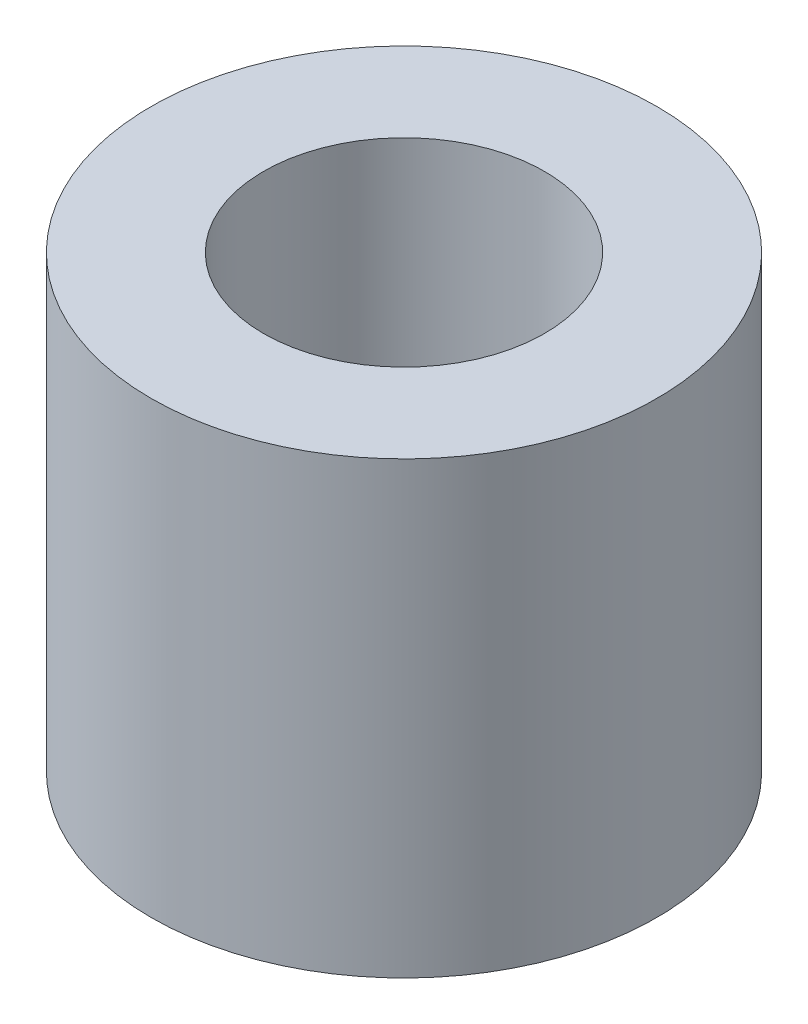
SolidWorks part; units mm, degrees
ref_plane "Front Plane" through (0, 0, 0) normal (0, 0, 1) x (1, 0, 0)
ref_plane "Top Plane" through (0, 0, 0) normal (0, 1, 0) x (1, 0, 0)
ref_plane "Right Plane" through (0, 0, 0) normal (1, 0, 0) x (0, 0, -1)
sketch "Sketch1" plane through (0, 0, 0) normal (0, 1, 0) x (1, 0, 0)
  circle A0 centre (0, 0) radius 4.5
  circle A1 centre (0, 0) radius 2.5
  dimension "D1" = 5
  dimension "D2" = 2
extrude "Boss-Extrude1" add sketch "Sketch1" along normal blind 8
